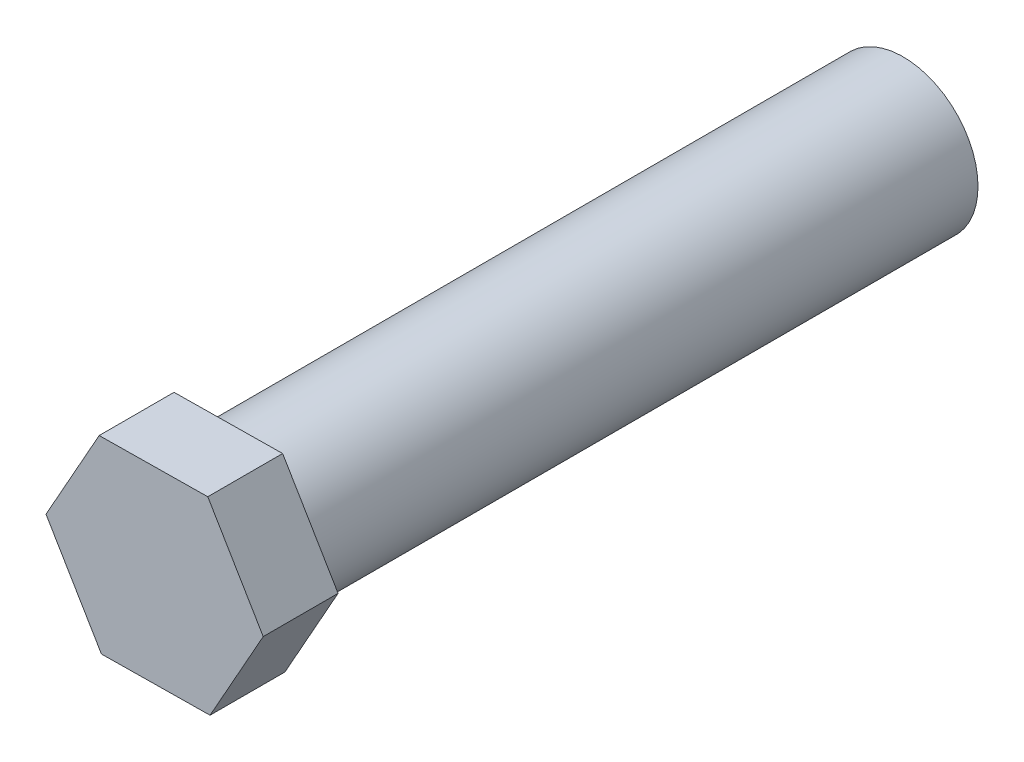
SolidWorks part; units mm, degrees
ref_plane "Front Plane" through (0, 0, 0) normal (0, 0, 1) x (1, 0, 0)
ref_plane "Top Plane" through (0, 0, 0) normal (0, 1, 0) x (1, 0, 0)
ref_plane "Right Plane" through (0, 0, 0) normal (1, 0, 0) x (0, 0, -1)
sketch "Sketch1" plane through (0, 0, 0) normal (0, 0, 1) x (1, 0, 0)
  circle A0 centre (0, 0) radius 2
extrude "Boss-Extrude1" add sketch "Sketch1" along normal blind 18
sketch "Sketch2" plane through (0, 0, 18) normal (0, 0, 1) x (1, 0, 0)
  line L1 (1.4811, -2.4957) -> (2.9019, 0.0348)
  line L2 (2.9019, 0.0348) -> (1.4208, 2.5306)
  line L3 (1.4208, 2.5306) -> (-1.4811, 2.4957)
  line L4 (-1.4811, 2.4957) -> (-2.9019, -0.0348)
  line L5 (-2.9019, -0.0348) -> (-1.4208, -2.5306)
  line L6 (-1.4208, -2.5306) -> (1.4811, -2.4957)
  circle A0 centre (0, 0) radius 2.5133 construction
extrude "Boss-Extrude2" add sketch "Sketch2" along normal blind 2
